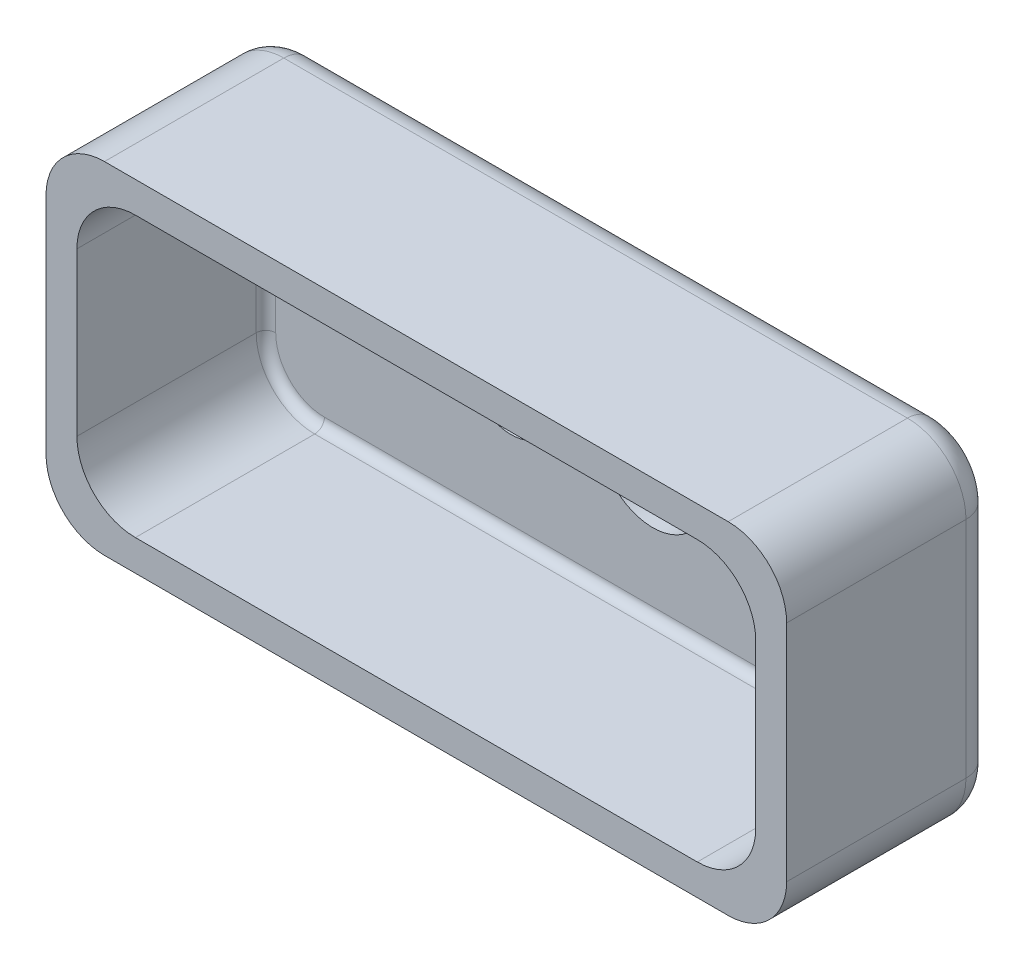
SolidWorks part; units mm, degrees
ref_plane "Front Plane" through (0, 0, 0) normal (0, 0, 1) x (1, 0, 0)
ref_plane "Top Plane" through (0, 0, 0) normal (0, 1, 0) x (1, 0, 0)
ref_plane "Right Plane" through (0, 0, 0) normal (1, 0, 0) x (0, 0, -1)
sketch "Sketch1" plane through (0, 0, 0) normal (0, 0, 1) x (1, 0, 0)
  line L1 (-337.1569, 207.6961) -> (422.8431, 207.6961)
  line L2 (-337.1569, 207.6961) -> (-337.1569, -142.3039)
  line L3 (-337.1569, -142.3039) -> (422.8431, -142.3039)
  line L4 (422.8431, 207.6961) -> (422.8431, -142.3039)
  dimension "D1" = 760
  dimension "D2" = 350
extrude "Boss-Extrude1" add sketch "Sketch1" along normal blind 38
sketch "Sketch2" plane through (0, 0, 38) normal (0, 0, 1) x (1, 0, 0)
  line L0 (422.8431, 207.6961) -> (422.8431, 24.6561)
  line L1 (422.8431, -142.3039) -> (422.8431, 207.6961) construction
  line L2 (422.8431, 24.6561) -> (245.4031, 24.6561)
  line L3 (245.4031, 24.6561) -> (91.4031, 24.6561)
  line L4 (91.4031, 24.6561) -> (-54.0069, 24.6561)
  circle A0 centre (245.4031, 24.6561) radius 65
  circle A1 centre (91.4031, 24.6561) radius 55
  circle A2 centre (-54.0069, 24.6561) radius 45
  dimension "D1" = 183.04
  dimension "D2" = 177.44
  dimension "D3" = 154
  dimension "D4" = 145.41
extrude "Cut-Extrude1" cut sketch "Sketch2" against normal through all
sketch "Sketch3" plane through (0, 0, 38) normal (0, 0, 1) x (1, 0, 0)
  line L0 (-54.0069, 24.6561) -> (-191.0869, 24.6561)
  line L1 (-191.0869, 24.6561) -> (-337.1569, 24.6561)
  line L2 (-337.1569, 207.6961) -> (-337.1569, -142.3039) construction
  circle A0 centre (-191.0869, 24.6561) radius 20
  dimension "D1" = 137.08
extrude "Cut-Extrude3" cut sketch "Sketch3" against normal through all contours L0 A0 L1 | L1 A0 L0
sketch "Sketch5" plane through (0, 0, 0) normal (0, 0, -1) x (-1, 0, 0)
  circle A0 centre (54.0069, 24.6561) radius 75
  circle A1 centre (-91.4031, 24.6561) radius 70
  circle A2 centre (191.0869, 24.6561) radius 40
  circle A3 centre (-91.4031, 24.6561) radius 60
  circle A4 centre (54.0069, 24.6561) radius 60
  circle A5 centre (191.0869, 24.6561) radius 30
  circle A6 centre (-91.4031, 84.6561) radius 3
  circle A7 centre (54.0069, 84.6561) radius 3
  circle A8 centre (191.0869, 54.6561) radius 3
  circle A9 centre (217.0676, 9.6561) radius 3
  circle A10 centre (165.1061, 9.6561) radius 3
  circle A11 centre (105.9684, -5.3439) radius 3
  circle A12 centre (2.0453, -5.3439) radius 3
  circle A13 centre (-39.4416, -5.3439) radius 3
  circle A14 centre (-143.3647, -5.3439) radius 3
  point P24 (191.0869, 24.6561)
  point P30 (54.0069, 24.6561)
  point P34 (-91.4031, 24.6561)
  circle M7 centre (191.0869, 24.6561) radius 20
  circle M8 centre (54.0069, 24.6561) radius 45
  circle M9 centre (-91.4031, 24.6561) radius 55
  dimension "D1" = 3
  dimension "D2" = 3
  dimension "D3" = 3
extrude "Cut-Extrude7" cut sketch "Sketch5" against normal blind 7 contours A14 A3 A13 A6 M9 | A1 A14 A3 A6 A13 | A0 A12 A4 A7 A11 | A12 A4 A11 A7 M8 | A2 A10 A5 A8 A9 | A10 A5 A9 A8 M7
sketch "Sketch7" plane through (0, 0, 0) normal (0, 0, -1) x (-1, 0, 0)
  circle A0 centre (-91.4031, 84.6561) radius 3
  circle A1 centre (-143.3647, -5.3439) radius 3
  circle A2 centre (-39.4416, -5.3439) radius 3
  circle A3 centre (2.0453, -5.3439) radius 3
  circle A4 centre (54.0069, 84.6561) radius 3
  circle A5 centre (105.9684, -5.3439) radius 3
  circle A6 centre (191.0869, 54.6561) radius 3
  circle A7 centre (165.1061, 9.6561) radius 3
  circle A8 centre (217.0676, 9.6561) radius 3
extrude "Cut-Extrude8" cut sketch "Sketch7" against normal through all
sketch "Sketch8" plane through (0, 0, 38) normal (0, 0, 1) x (1, 0, 0)
  line L1 (-337.1569, 207.6961) -> (422.8431, 207.6961)
  line L2 (-337.1569, 207.6961) -> (-337.1569, -142.3039)
  line L3 (-337.1569, -142.3039) -> (422.8431, -142.3039)
  line L4 (422.8431, 207.6961) -> (422.8431, -142.3039)
extrude "Cut-Extrude9" cut sketch "Sketch8" against normal blind 18
sketch "Sketch9" plane through (0, 0, 20) normal (0, 0, 1) x (1, 0, 0)
  line L1 (-277.1569, 207.6961) -> (362.8431, 207.6961)
  line L2 (-337.1569, 147.6961) -> (-337.1569, -82.3039)
  line L3 (-277.1569, -142.3039) -> (362.8431, -142.3039)
  line L4 (422.8431, 147.6961) -> (422.8431, -82.3039)
  arc A0 (362.8431, -142.3039) -> (422.8431, -82.3039) centre (362.8431, -82.3039) ccw
  arc A1 (422.8431, 147.6961) -> (362.8431, 207.6961) centre (362.8431, 147.6961) ccw
  arc A2 (-277.1569, -142.3039) -> (-337.1569, -82.3039) centre (-277.1569, -82.3039) cw
  arc A3 (-337.1569, 147.6961) -> (-277.1569, 207.6961) centre (-277.1569, 147.6961) cw
  point P8 (422.8431, -142.3039)
  point P15 (-337.1569, 207.6961)
  dimension "D1" = 60
extrude "Cut-Extrude10" cut sketch "Sketch9" against normal through all flip side to cut
sketch "Sketch10" plane through (0, 0, 20) normal (0, 0, 1) x (1, 0, 0)
  line L1 (-277.1569, 207.6961) -> (362.8431, 207.6961)
  line L2 (-337.1569, 147.6961) -> (-337.1569, -82.3039)
  line L3 (-245.4411, 175.9803) -> (331.1274, 175.9803)
  line L4 (-305.4411, 115.9803) -> (-305.4411, -50.5882)
  line L5 (-245.4411, -110.5882) -> (331.1274, -110.5882)
  line L6 (391.1274, 115.9803) -> (391.1274, -50.5882)
  line L7 (-277.1569, -142.3039) -> (362.8431, -142.3039)
  line L8 (422.8431, 147.6961) -> (422.8431, -82.3039)
  arc A2 (-305.4411, -50.5882) -> (-245.4411, -110.5882) centre (-245.4411, -50.5882) ccw
  arc A3 (331.1274, -110.5882) -> (391.1274, -50.5882) centre (331.1274, -50.5882) ccw
  arc A4 (391.1274, 115.9803) -> (331.1274, 175.9803) centre (331.1274, 115.9803) ccw
  arc A5 (-245.4411, 175.9803) -> (-305.4411, 115.9803) centre (-245.4411, 115.9803) ccw
  arc A6 (362.8431, -142.3039) -> (422.8431, -82.3039) centre (362.8431, -82.3039) ccw
  arc A7 (422.8431, 147.6961) -> (362.8431, 207.6961) centre (362.8431, 147.6961) ccw
  arc A8 (-277.1569, -142.3039) -> (-337.1569, -82.3039) centre (-277.1569, -82.3039) cw
  arc A9 (-337.1569, 147.6961) -> (-277.1569, 207.6961) centre (-277.1569, 147.6961) cw
  dimension "D1" = 60
  dimension "D2" = 60
extrude "Boss-Extrude2" add sketch "Sketch10" along normal blind 194
fillet "Fillet1" radius 10 8 edges at (373.5538, 158.4068, 20) (391.1274, 32.6961, 20) (373.5538, -93.0146, 20) (42.8431, -110.5882, 20) (-287.8675, -93.0146, 20) (-305.4411, 32.6961, 20) (-287.8675, 158.4068, 20) (42.8431, 175.9803, 20)
sketch "Sketch11" plane through (0, 0, 0) normal (0, 0, -1) x (-1, 0, 0)
  circle A0 centre (-245.4031, 24.6561) radius 80
  circle A1 centre (-245.4031, 24.6561) radius 65
  circle A2 centre (-245.4031, 24.6561) radius 70
  circle A3 centre (-245.4031, 94.6561) radius 3
  circle A4 centre (-184.7814, -10.3439) radius 3
  circle A5 centre (-306.0249, -10.3439) radius 3
  point P13 (-245.4031, 24.6561)
  circle M6 centre (-245.4031, 24.6561) radius 65
  dimension "D1" = 3
sketch "Sketch12" plane through (0, 0, 7) normal (0, 0, -1) x (-1, 0, 0)
  circle A0 centre (191.0869, 24.6561) radius 40
  circle A1 centre (191.0869, 24.6561) radius 20
  circle A2 centre (191.0869, 54.6561) radius 3
  circle A3 centre (165.1061, 9.6561) radius 3
  circle A4 centre (217.0676, 9.6561) radius 3
extrude "Boss-Extrude4" add sketch "Sketch12" along normal through all and the other way blind 2
sketch "Sketch13" plane through (0, 0, 0) normal (0, 0, -1) x (-1, 0, 0)
  circle A0 centre (191.0869, 54.6561) radius 3
  circle A1 centre (217.0676, 9.6561) radius 3
  circle A2 centre (165.1061, 9.6561) radius 3
extrude "Boss-Extrude8" add sketch "Sketch13" against normal up to surface (20 mm away) up to face at (42.8431, 32.6961, 20)
extrude "Cut-Extrude11" cut sketch "Sketch11" against normal blind 7 contours A0 A5 A2 A3 A4 | A5 A2 A4 A3 M6
sketch "Sketch15" plane through (0, 0, 0) normal (0, 0, -1) x (-1, 0, 0)
  circle A1 centre (-245.4031, 94.6561) radius 3
  circle A2 centre (-306.0249, -10.3439) radius 3
  circle A3 centre (-184.7814, -10.3439) radius 3
extrude "Cut-Extrude12" cut sketch "Sketch15" against normal through all
fillet "Fillet2" radius 30 8 edges at (405.2695, 190.1225, 0) (422.8431, 32.6961, 0) (405.2695, -124.7303, 0) (42.8431, -142.3039, 0) (-319.5833, -124.7303, 0) (-337.1569, 32.6961, 0) (-319.5833, 190.1225, 0) (42.8431, 207.6961, 0)
